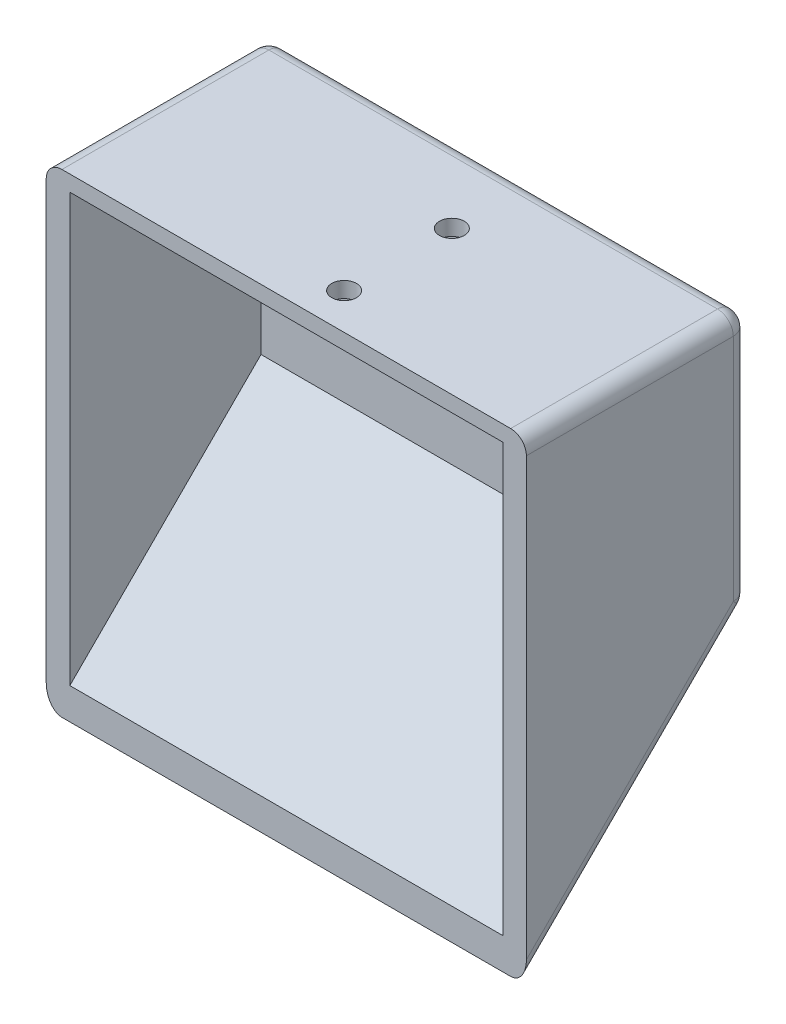
SolidWorks part; units mm, degrees
ref_plane "Front" through (0, 0, 0) normal (0, 0, 1) x (1, 0, 0)
ref_plane "Top" through (0, 0, 0) normal (0, 1, 0) x (1, 0, 0)
ref_plane "Right" through (0, 0, 0) normal (1, 0, 0) x (0, 0, -1)
sketch "Sketch1" plane through (0, 0, 0) normal (0, 0, 1) x (1, 0, 0)
  line L1 (34.925, -19.05) -> (-34.925, -19.05)
  line L2 (34.925, -19.05) -> (34.925, 19.05)
  line L3 (34.925, 19.05) -> (-34.925, 19.05)
  line L4 (-34.925, -19.05) -> (-34.925, 19.05)
  line L5 (34.925, -19.05) -> (-34.925, 19.05) construction
  line L6 (34.925, 19.05) -> (-34.925, -19.05) construction
  point P0 (0, 0)
  dimension "D1" = 38.1
  dimension "D2" = 69.85
extrude "Boss-Extrude1" add sketch "Sketch1" along normal blind 5.08
sketch "Sketch2" plane through (-34.925, 0, 0) normal (-1, 0, 0) x (0, 0, 1)
  line L0 (5.08, -19.05) -> (20.2004, -34.1704)
  line L1 (5.08, 19.05) -> (5.08, -19.05) construction
  line L2 (0, -19.05) -> (35.921, -54.971)
  line L3 (20.2004, -34.1704) -> (29.5565, -43.5265)
  line L4 (35.921, -54.971) -> (35.921, -49.891)
  line L5 (29.5565, -43.5265) -> (35.921, -49.891)
  line L6 (0, -19.05) -> (5.08, -19.05)
  dimension "D1" = 135
  dimension "D2" = 50.8
extrude "Boss-Extrude2" add sketch "Sketch2" against normal up to surface (69.85 mm away) up to face at (34.925, 0, 2.54)
sketch "Sketch3" plane through (34.925, 0, 0) normal (1, 0, 0) x (0, 0, -1)
  line L0 (-35.921, -54.971) -> (0, -19.05)
  line L1 (0, -19.05) -> (0, 19.05)
  line L2 (0, 19.05) -> (-35.921, 19.05)
  line L3 (-35.921, 19.05) -> (-35.921, -54.971)
extrude "Boss-Extrude3" add sketch "Sketch3" along normal blind 3.81
sketch "Sketch5" plane through (-34.925, 0, 0) normal (-1, 0, 0) x (0, 0, 1)
  line L0 (5.08, 19.05) -> (35.921, 19.05)
  line L1 (35.921, 19.05) -> (35.921, -54.971)
  line L2 (0, -19.05) -> (35.921, -54.971)
  line L3 (0, -19.05) -> (0, 19.05)
  line L4 (0, 19.05) -> (5.08, 19.05)
extrude "Boss-Extrude4" add sketch "Sketch5" along normal blind 3.81
sketch "Sketch6" plane through (0, 19.05, 0) normal (0, 1, 0) x (1, 0, 0)
  line L1 (38.735, 0) -> (-38.735, 0)
  line L2 (38.735, 0) -> (38.735, -35.921)
  line L3 (38.735, -35.921) -> (-38.735, -35.921)
  line L4 (-38.735, 0) -> (-38.735, -35.921)
extrude "Boss-Extrude5" add sketch "Sketch6" along normal blind 2.54
fillet "Fillet1" radius 2.54 8 edges at (-38.735, -37.0105, 17.9605) (0, -19.05, 0) (38.735, -37.0105, 17.9605) (38.735, 21.59, 17.9605) (38.735, 1.27, 0) (-38.735, 1.27, 0) (-38.735, 21.59, 17.9605) (0, 21.59, 0)
sketch "Sketch7" plane through (0, 21.59, 0) normal (0, 1, 0) x (1, 0, 0)
  line L0 (-4.6965, -2.54) -> (-4.6965, -35.921)
  line L1 (36.195, -2.54) -> (-36.195, -2.54) construction
  line L2 (-36.195, -35.921) -> (36.195, -35.921) construction
  line L3 (-36.195, -2.54) -> (-36.195, -35.921) construction
  line L4 (3.4839, -2.54) -> (3.4839, -35.921)
  circle A0 centre (3.4839, -30.079) radius 2
  circle A1 centre (3.4839, -12.7) radius 2
  dimension "D3" = 4
  dimension "D4" = 4
  dimension "D1" = 31.4985
  dimension "D2" = 8.1803
  dimension "D5" = 5.842
  dimension "D6" = 10.16
extrude "Cut-Extrude1" cut sketch "Sketch7" against normal up to surface (2.54 mm away) contours L4 A1 | L4 A1 | L4 A0 | L4 A0 up to face at (0, 19.05, 20.5005)
